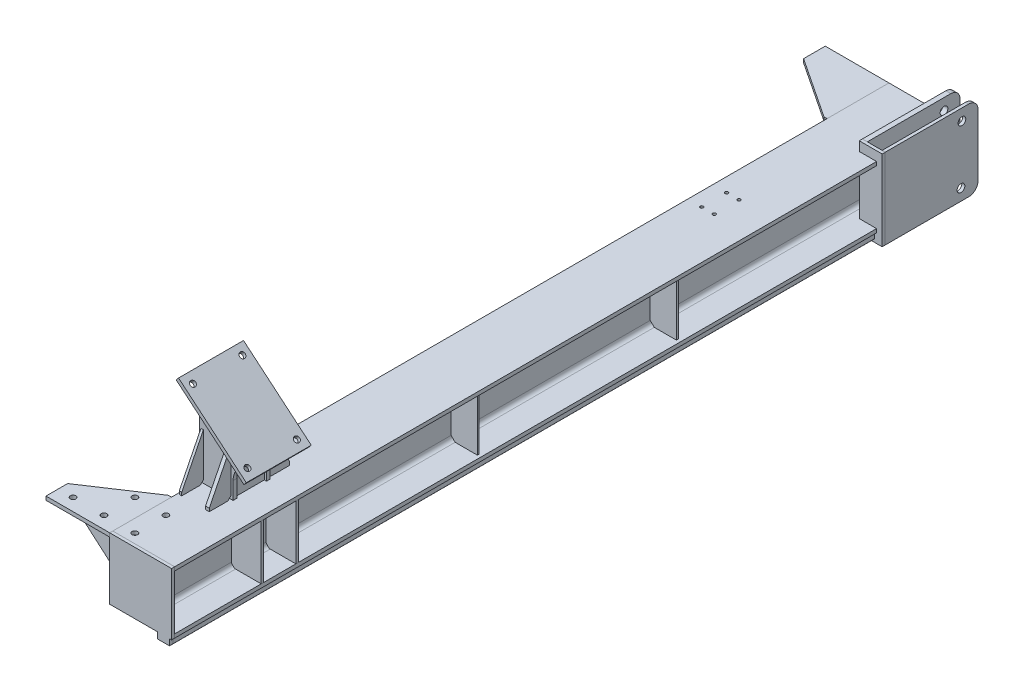
SolidWorks part; units mm, degrees
material "普通碳钢"
ref_plane "前视基准面" through (0, 0, 0) normal (0, 0, 1) x (1, 0, 0)
ref_plane "上视基准面" through (0, 0, 0) normal (0, 1, 0) x (1, 0, 0)
ref_plane "右视基准面" through (0, 0, 0) normal (1, 0, 0) x (0, 0, -1)
sketch "草图1" plane through (0, 0, 0) normal (1, 0, 0) x (0, 0, -1)
  line L0 (0, 0) -> (2410, 0)
  dimension "D1" = 2410
other "H型钢 HW200A(1)"
ref_plane "基准面1" through (0, 0, 0) normal (0, 0, -1) x (1, 0, 0)
sketch "草图14" plane through (0, 0, 0) normal (0, 0, -1) x (1, 0, 0)
  line L0 (-100, -100) -> (100, -100)
  line L1 (100, -100) -> (100, -88)
  line L2 (100, -88) -> (17, -88)
  line L3 (4, -75) -> (4, 75)
  line L4 (17, 88) -> (100, 88)
  line L5 (100, 88) -> (100, 100)
  line L6 (100, 100) -> (-100, 100)
  line L7 (0, 100) -> (0, -100) construction
  line L11 (0, 60) -> (0, 100) construction
  line L14 (-100, -100) -> (-100, -88)
  line L15 (-100, -88) -> (-17, -88)
  line L16 (-4, -75) -> (-4, 75)
  line L17 (-17, 88) -> (-100, 88)
  line L18 (-100, 88) -> (-100, 100)
  arc A2 (17, -88) -> (4, -75) centre (17, -75) cw
  arc A3 (4, 75) -> (17, 88) centre (17, 75) cw
  arc A5 (-17, -88) -> (-4, -75) centre (-17, -75) ccw
  arc A6 (-4, 75) -> (-17, 88) centre (-17, 75) ccw
  point P2 (0, 0)
  point P38 (0, 0)
  point P39 (100, 100)
  point P40 (100, -100)
  point P41 (-100, -100)
  dimension "D8" = 13
  dimension "D1" = 8
  dimension "D2" = 12
  dimension "D3" = 200
  dimension "D4" = 200
  dimension "D9" = 0
sketch "草图12" plane through (0, 100, 0) normal (0, 1, 0) x (1, 0, 0)
  line L4 (94, 2410) -> (94, 0)
  line L5 (94, 2410) -> (94, 0)
  dimension "D1" = 6
other "折弯轨道"
ref_plane "基准面2" through (94, 130, -2410) normal (0, 0, 1) x (1, 0, 0)
sketch "草图13" plane through (94, 130, -2410) normal (0, 0, 1) x (1, 0, 0)
  line L7 (-38, 0) -> (-2, 0)
  line L8 (-40, -2) -> (-40, -30)
  line L9 (0, -2) -> (0, -30)
  line L20 (-40, -30) -> (0, -30)
  line L21 (-194, 0) -> (6, 0) construction
  arc A7 (-2, 0) -> (0, -2) centre (-2, -2) cw
  arc A8 (-38, 0) -> (-40, -2) centre (-38, -2) ccw
  point P11 (25, 0)
  point P21 (0, 0)
  dimension "D4" = 2
  dimension "D1" = 30
  dimension "D2" = 40
  dimension "D5" = 6
mirror "镜向1" about plane through (0, 0, 0) normal (0, 1, 0) of bodies 108
sketch "草图16" plane through (0, 0, 0) normal (0, 0, 1) x (1, 0, 0)
  line L0 (94, -100) -> (100, -100)
  line L1 (-100, 100) -> (54, 100)
  line L2 (-100, 100) -> (-100, -100)
  line L3 (-100, -100) -> (54, -100)
  line L4 (100, 100) -> (100, -100)
  line L5 (94, -100) -> (94, -128)
  line L6 (94, 128) -> (94, 100)
  line L7 (54, 128) -> (54, 100)
  line L8 (94, 100) -> (100, 100)
  line L9 (92, 130) -> (56, 130) construction
  line L10 (54, 128) -> (54, 100) construction
  line L11 (100, -100) -> (-100, -100) construction
  line L12 (-100, 100) -> (100, 100) construction
  line L16 (92, 130) -> (56, 130)
  line L32 (92, -130) -> (56, -130)
  line L33 (54, -128) -> (54, -100)
  arc A0 (54, -128) -> (56, -130) centre (56, -128) ccw construction
  arc A1 (92, -130) -> (94, -128) centre (92, -128) ccw construction
  arc A2 (56, 130) -> (54, 128) centre (56, 128) ccw construction
  arc A3 (94, 128) -> (92, 130) centre (92, 128) ccw construction
  arc A4 (56, 130) -> (54, 128) centre (56, 128) ccw
  arc A7 (94, 128) -> (92, 130) centre (92, 128) ccw
  arc A17 (92, -130) -> (94, -128) centre (92, -128) ccw
  arc A18 (54, -128) -> (56, -130) centre (56, -128) ccw
  dimension "D1" = 30
extrude "凸台-拉伸1" add sketch "草图16" along normal blind 10 separate body contours L4 L0 L5 A17 L32 A18 L33 L3 L2 L1 L7 A4 L16 A7 L6 L8
sketch "草图17" plane through (0, 130, 0) normal (0, 1, 0) x (1, 0, 0)
  line L8 (-100, 2410) -> (100, 2410) construction
  line L9 (44, 2410) -> (100, 2410)
  line L11 (44, 2270) -> (100, 2270)
  line L12 (100, 2410) -> (100, 0) construction
  line L13 (100, 2410) -> (100, 2270)
  line L14 (44, 2354) -> (44, 0) construction
  line L15 (44, 2410) -> (44, 2270)
  line L17 (-100, 2410) -> (100, 2410) construction
  line L18 (-100, 2270) -> (100, 2270) construction
  line L19 (-100, 2354) -> (44, 2354) construction
  line L20 (100, 2410) -> (100, 0) construction
  dimension "D1" = 140
  dimension "D2" = 56
extrude "切除-拉伸1" cut sketch "草图17" against normal up to surface (260 mm away)
sketch "草图18" plane through (0, 130, 0) normal (0, 1, 0) x (1, 0, 0)
  line L0 (100, 2270) -> (100, 0) construction
  line L1 (44, 2580) -> (60, 2580)
  line L2 (44, 2580) -> (44, 2280)
  line L4 (60, 2580) -> (60, 2280)
  line L5 (100, 2270) -> (44, 2270) construction
  line L6 (44, 2280) -> (60, 2280)
  line L8 (118, 2280) -> (118, 2580)
  line L9 (118, 2580) -> (108, 2580)
  line L10 (108, 2280) -> (108, 2580)
  line L11 (108, 2280) -> (118, 2280)
  line L14 (44, 2270) -> (44, 2410) construction
  point P17 (34, 2400)
  dimension "D1" = 16
  dimension "D2" = 10
  dimension "D3" = 10
  dimension "D4" = 10
  dimension "D5" = 18
  dimension "D6" = 300
extrude "凸台-拉伸2" add sketch "草图18" against normal up to surface (260 mm away) separate body up to face at (74, -130, -1135)
fillet "圆角1" radius 30 2 edges at (113, -130, -2580) (113, 130, -2580)
fillet "圆角2" radius 30 2 edges at (52, -130, -2580) (52, 130, -2580)
sketch "草图19" plane through (0, 130, 0) normal (0, 1, 0) x (1, 0, 0)
  line L1 (44, 2280) -> (118, 2280)
  line L2 (44, 2280) -> (44, 2270)
  line L3 (44, 2270) -> (118, 2270)
  line L4 (118, 2280) -> (118, 2270)
  line L6 (100, 2270) -> (100, 0) construction
  line L7 (100, 2270) -> (44, 2270) construction
  dimension "D1" = 18
extrude "凸台-拉伸3" add sketch "草图19" against normal up to surface (260 mm away) separate body up to face at (74, -130, -1135)
sketch "草图20" plane through (118, 0, 0) normal (1, 0, 0) x (0, 0, -1)
  line L0 (2280, -130) -> (2280, 130) construction
  line L1 (2280, -130) -> (2280, 130) construction
  line L2 (2280, 130) -> (2550, 130) construction
  line L3 (2550, -130) -> (2280, -130) construction
  circle A0 centre (2528, 93) radius 12.5
  circle A1 centre (2525, -93) radius 12.5
  dimension "D1" = 248
  dimension "D3" = 25
  dimension "D4" = 25
  dimension "D2" = 245
  dimension "D5" = 37
  dimension "D6" = 37
extrude "切除-拉伸2" cut sketch "草图20" against normal up to surface (74 mm away) contours A1
ref_plane "基准面3" through (0, 0, -2480) normal (0, 0, -1) x (-1, 0, 0)
sketch "草图21" plane through (0, 0, -2480) normal (0, 0, -1) x (-1, 0, 0)
  line L0 (-60, 130) -> (-60, 100) construction
  line L1 (-60, 55) -> (-108, 55)
  line L2 (-60, 55) -> (-60, -55)
  line L3 (-60, -55) -> (-108, -55)
  line L4 (-108, 55) -> (-108, -55)
  line L5 (-108, -130) -> (-108, -100) construction
  line L6 (-118, 130) -> (-44, 130) construction
  line L7 (-118, 130) -> (-44, 130) construction
  line L8 (-44, -130) -> (-118, -130) construction
  line L9 (-44, -130) -> (-118, -130) construction
  dimension "D1" = 75
  dimension "D2" = 75
extrude "凸台-拉伸5" add sketch "草图21" against normal blind 8 separate body
ref_plane "基准面4" through (0, 0, -340) normal (0, 0, 1) x (1, 0, 0)
sketch "草图23" plane through (0, 0, -340) normal (0, 0, 1) x (1, 0, 0)
  line L6 (89.0887, 206.9702) -> (-130, 390.8075)
  line L7 (96.8022, 216.1627) -> (-122.2865, 400)
  line L8 (89.0887, 206.9702) -> (96.8022, 216.1627)
  line L9 (-130, 390.8075) -> (-122.2865, 400)
  line L11 (-100, 100) -> (44, 100) construction
  line L12 (-100, 100) -> (54, 100) construction
  line L13 (-100, 100) -> (-100, -100) construction
  dimension "D1" = 286
  dimension "D2" = 12
  dimension "D3" = 30
  dimension "D4" = 40
  dimension "D5" = 300
extrude "凸台-拉伸6" add sketch "草图23" along normal mid plane 210 separate body
sketch "草图25" plane through (146.4357, 174.5153, 0) normal (0.6428, 0.766, 0) x (0.766, -0.6428, 0)
  line L2 (-64.792, 420) -> (-350.792, 420)
  line L3 (-64.792, 420) -> (-350.792, 420) construction
  line L5 (-64.792, 260) -> (-350.792, 260)
  line L6 (-64.792, 260) -> (-350.792, 260) construction
  line L8 (-322.792, 235) -> (-322.792, 445)
  line L9 (-322.792, 235) -> (-322.792, 445) construction
  line L12 (-92.792, 235) -> (-92.792, 445)
  line L13 (-92.792, 235) -> (-92.792, 445) construction
  circle A0 centre (-322.792, 420) radius 9
  circle A1 centre (-92.792, 420) radius 9
  circle A2 centre (-92.792, 260) radius 9
  circle A3 centre (-322.792, 260) radius 9
  dimension "D5" = 18
  dimension "D6" = 18
  dimension "D7" = 18
  dimension "D8" = 18
  dimension "D1" = 25
  dimension "D2" = 25
  dimension "D3" = 28
  dimension "D4" = 28
extrude "切除-拉伸4" cut sketch "草图25" against normal up to next (12 mm away)
sketch "草图24" plane through (0, 0, -340) normal (0, 0, 1) x (1, 0, 0)
  line L0 (-100, 100) -> (54, 100) construction
  line L1 (2, 100) -> (-10, 100)
  line L2 (2, 100) -> (2, 280.0463)
  line L3 (-4, 285.0809) -> (-10, 285.0809)
  line L4 (-10, 100) -> (-10, 285.0809)
  line L5 (2, 280.0463) -> (-4, 285.0809)
  line L7 (-130, 390.8075) -> (89.0887, 206.9702) construction
  line L9 (-100, 88) -> (-100, 100) construction
  point P2 (2, 285.0809)
  dimension "D1" = 12
  dimension "D2" = 6
  dimension "D3" = 90
extrude "凸台-拉伸7" add sketch "草图24" along normal mid plane 96 separate body
sketch "草图26" plane through (0, 0, -388) normal (0, 0, -1) x (-1, 0, 0)
  line L0 (-59.0887, 232.1432) -> (100, 365.6345)
  line L1 (100, 365.6345) -> (100, 100)
  line L2 (-59.0887, 232.1432) -> (-59.0887, 154.6102) construction
  line L3 (130, 390.8075) -> (130, -58) construction
  line L4 (-89.0887, 206.9702) -> (-89.0887, 63.1666) construction
  line L5 (-44, 100) -> (-44, 297.8719) construction
  line L6 (-9, 100) -> (-9, 297.8719) construction
  line L8 (-9, 100) -> (100, 100)
  line L10 (100, 88) -> (17, 88)
  line L14 (17, -88) -> (100, -88)
  line L15 (17, 88) -> (4, 75)
  line L16 (4, 75) -> (4, -75)
  line L17 (4, -75) -> (17, -88)
  line L18 (130, 390.8075) -> (130, 142.1948) construction
  line L19 (130, 390.8075) -> (-89.0887, 206.9702) construction
  line L20 (-9, 100) -> (-9, 155.8505)
  line L21 (-25.7297, 197.4159) -> (-59.0887, 232.1432)
  line L22 (100, 88) -> (100, -88)
  arc A0 (-9, 155.8505) -> (-25.7297, 197.4159) centre (-69, 155.8505) ccw
  point P11 (-9, 180)
  dimension "D4" = 60
  dimension "D1" = 30
  dimension "D2" = 35
  dimension "D3" = 80
extrude "凸台-拉伸8" add sketch "草图26" along normal blind 12 separate body
sketch "草图27" plane through (0, 0, -292) normal (0, 0, 1) x (1, 0, 0)
  line L4 (25.7297, 197.4159) -> (59.0887, 232.1432)
  line L5 (59.0887, 232.1432) -> (-100, 365.6345)
  line L6 (-100, 88) -> (-100, -88)
  line L7 (-100, 88) -> (-100, -88)
  line L8 (-100, 365.6345) -> (-100, 100)
  line L9 (-100, 100) -> (9, 100)
  line L11 (59.0887, 232.1432) -> (-100, 365.6345)
  line L12 (-100, 365.6345) -> (-100, 100)
  line L13 (-100, -88) -> (-17, -88)
  line L14 (-17, -88) -> (-4, -75)
  line L15 (-4, -75) -> (-4, 75)
  line L16 (-4, 75) -> (-17, 88)
  line L17 (-17, 88) -> (-100, 88)
  line L18 (-100, 100) -> (9, 100)
  line L23 (-100, -88) -> (-17, -88)
  line L24 (-17, -88) -> (-4, -75)
  line L25 (-4, -75) -> (-4, 75)
  line L26 (-4, 75) -> (-17, 88)
  line L27 (-17, 88) -> (-100, 88)
  line L29 (25.7297, 197.4159) -> (59.0887, 232.1432)
  line L30 (9, 100) -> (9, 155.8505)
  line L31 (9, 100) -> (9, 155.8505)
  arc A1 (25.7297, 197.4159) -> (9, 155.8505) centre (69, 155.8505) ccw
  arc A2 (25.7297, 197.4159) -> (9, 155.8505) centre (69, 155.8505) ccw
  dimension "D1" = 0
  dimension "D2" = 0
extrude "凸台-拉伸11" add sketch "草图27" along normal blind 12 separate body contours L23 L24 L25 L26 L27 L7 | L11 L12 L18 L31 A2 L29
sketch "草图32" plane through (0, 0, 10) normal (0, 0, 1) x (1, 0, 0)
  line L0 (92, 130) -> (56, 130) construction
  line L1 (54, 100) -> (94, 100)
  line L2 (54, 100) -> (54, 130)
  line L3 (54, 130) -> (94, 130)
  line L4 (94, 100) -> (94, 130)
  line L5 (94, 128) -> (94, 100) construction
extrude "切除-拉伸9" cut sketch "草图32" against normal up to surface (2280 mm away) up to face at (81, 0, -2270)
sketch "草图33" plane through (0, 0, -2410) normal (0, 0, -1) x (-1, 0, 0)
  line L0 (-44, 100) -> (-44, 88)
  line L1 (-44, -88) -> (-44, -100)
  line L2 (-44, 100) -> (-44, 88) construction
  line L12 (100, 100) -> (-44, 100)
  line L13 (-44, 100) -> (-44, 88)
  line L14 (-44, 88) -> (-17, 88)
  line L15 (-4, 75) -> (-4, -75)
  line L16 (-17, -88) -> (-44, -88)
  line L17 (-44, -88) -> (-44, -100)
  line L18 (-44, -100) -> (100, -100)
  line L19 (100, -100) -> (100, -88)
  line L20 (100, -88) -> (17, -88)
  line L21 (4, -75) -> (4, 75)
  line L22 (17, 88) -> (100, 88)
  line L23 (100, 88) -> (100, 100)
  line L24 (100, 100) -> (-44, 100)
  line L26 (-44, 88) -> (-17, 88)
  line L27 (-4, 75) -> (-4, -75)
  line L28 (-17, -88) -> (-44, -88)
  line L30 (-44, -100) -> (100, -100)
  line L31 (100, -100) -> (100, -88)
  line L32 (100, -88) -> (17, -88)
  line L33 (4, -75) -> (4, 75)
  line L34 (17, 88) -> (100, 88)
  line L35 (100, 88) -> (100, 100)
  arc A4 (-4, 75) -> (-17, 88) centre (-17, 75) ccw
  arc A5 (-17, -88) -> (-4, -75) centre (-17, -75) ccw
  arc A6 (4, -75) -> (17, -88) centre (17, -75) ccw
  arc A7 (17, 88) -> (4, 75) centre (17, 75) ccw
  arc A8 (-4, 75) -> (-17, 88) centre (-17, 75) ccw
  arc A9 (-17, -88) -> (-4, -75) centre (-17, -75) ccw
  arc A10 (4, -75) -> (17, -88) centre (17, -75) ccw
  arc A11 (17, 88) -> (4, 75) centre (17, 75) ccw
  dimension "D1" = 0
extrude "凸台-拉伸12" add sketch "草图33" along normal blind 100
sketch "草图34" plane through (0, 88, 0) normal (0, -1, 0) x (1, 0, 0)
  line L0 (-306, 10) -> (-100, 10)
  line L1 (-100, 10) -> (-100, -190)
  line L2 (-100, -2510) -> (-100, 0) construction
  line L3 (-100, -190) -> (-110, -190)
  line L4 (-110, -190) -> (-306, -60)
  line L5 (-306, -60) -> (-306, 10)
  line L6 (-100, 10) -> (100, 10) construction
  dimension "D1" = 200
  dimension "D2" = 10
  dimension "D3" = 206
  dimension "D4" = 70
extrude "凸台-拉伸13" add sketch "草图34" against normal up to surface (12 mm away) separate body up to face at (14.6667, 100, -1593.3333)
sketch "草图35" plane through (0, 88, 0) normal (0, -1, 0) x (1, 0, 0)
  line L0 (-100, -2510) -> (-306, -2510)
  line L1 (-100, -2510) -> (-100, 0) construction
  line L2 (-306, -2510) -> (-306, -2440)
  line L3 (-306, -2440) -> (-110, -2310)
  line L4 (-110, -2310) -> (-100, -2310)
  line L5 (-100, -2310) -> (-100, -2510)
  line L6 (-17, -2510) -> (-100, -2510) construction
  dimension "D1" = 200
  dimension "D2" = 10
  dimension "D3" = 206
  dimension "D4" = 70
extrude "凸台-拉伸14" add sketch "草图35" against normal up to surface (12 mm away) separate body up to face at (14.6667, 100, -1593.3333)
ref_plane "基准面5" through (0, 0, -60) normal (0, 0, 1) x (1, 0, 0)
sketch "草图36" plane through (0, 0, -60) normal (0, 0, 1) x (1, 0, 0)
  line L4 (-17, 88) -> (-100, 88) construction
  line L5 (-95, 88) -> (-297, 88)
  line L9 (-95, 88) -> (-95, -88)
  line L10 (-95, -88) -> (-105, -88)
  line L11 (-105, -88) -> (-297, 78)
  line L12 (-100, 100) -> (-100, -100) construction
  line L13 (-100, -88) -> (-17, -88) construction
  line L24 (-297, 88) -> (-297, 78)
  dimension "D2" = 10
  dimension "D1" = 280
  dimension "D3" = 10
  dimension "D4" = 5
extrude "凸台-拉伸15" add sketch "草图36" along normal blind 10 separate body
ref_plane "基准面6" through (0, 0, -2440) normal (0, 0, -1) x (-1, 0, 0)
sketch "草图37" plane through (0, 0, -2440) normal (0, 0, -1) x (-1, 0, 0)
  line L5 (95, 88) -> (95, -88)
  line L6 (95, 88) -> (95, -88)
  line L7 (95, -88) -> (105, -88)
  line L8 (95, -88) -> (105, -88)
  line L9 (105, -88) -> (297, 78)
  line L10 (105, -88) -> (297, 78)
  line L12 (297, 78) -> (297, 88)
  line L13 (297, 88) -> (95, 88)
  line L19 (297, 78) -> (297, 88)
  line L20 (297, 88) -> (95, 88)
  dimension "D1" = 0
extrude "凸台-拉伸16" add sketch "草图37" along normal blind 10 separate body
sketch "草图38" plane through (0, 88, 0) normal (0, -1, 0) x (-1, 0, 0)
  line L0 (-47.2565, 2470) -> (306, 2470) construction
  line L1 (306, 2440) -> (306, 2510) construction
  line L2 (306, 2510) -> (100, 2510) construction
  line L4 (58.5, 2510) -> (58.5, 2450) construction
  line L5 (17, 2510) -> (100, 2510) construction
  line L6 (297, 2450) -> (95, 2450) construction
  line L7 (158.5, 2510) -> (158.5, 2342.1684) construction
  line L8 (258.5, 2510) -> (258.5, 2450) construction
  line L9 (-47.2565, 2370) -> (306, 2370) construction
  line L10 (58.5, 2450) -> (58.5, 2313.7396) construction
  line L11 (110, 2310) -> (306, 2440) construction
  circle A0 centre (58.5, 2470) radius 9
  circle A1 centre (158.5, 2470) radius 9
  circle A2 centre (258.5, 2470) radius 9
  circle A3 centre (58.5, 2370) radius 9
  circle A4 centre (158.5, 2370) radius 9
  dimension "D4" = 18
  dimension "D5" = 18
  dimension "D6" = 18
  dimension "D8" = 18
  dimension "D9" = 18
  dimension "D1" = 40
  dimension "D2" = 100
  dimension "D3" = 100
  dimension "D7" = 100
extrude "切除-拉伸10" cut sketch "草图38" against normal blind 10
sketch "草图39" plane through (0, 88, 0) normal (0, -1, 0) x (1, 0, 0)
  line L0 (-17, -30) -> (-306, -30) construction
  line L1 (-17, -2510) -> (-17, 0) construction
  line L2 (-306, 10) -> (-306, -60) construction
  line L3 (-17, -130) -> (-200.4615, -130) construction
  line L4 (-306, -60) -> (-110, -190) construction
  line L5 (-58.5, 0) -> (-58.5, -170.5835) construction
  line L6 (-17, 0) -> (-100, 0) construction
  line L8 (-158.5, 10) -> (-158.5, -158.7816) construction
  line L9 (-100, 10) -> (-306, 10) construction
  line L10 (-258.5, 10) -> (-258.5, -80.1176) construction
  circle A0 centre (-258.5, -30) radius 9
  circle A1 centre (-158.5, -30) radius 9
  circle A2 centre (-58.5, -30) radius 9
  circle A3 centre (-58.5, -130) radius 9
  circle A4 centre (-158.5, -130) radius 9
  dimension "D5" = 18
  dimension "D6" = 18
  dimension "D7" = 18
  dimension "D8" = 18
  dimension "D9" = 18
  dimension "D1" = 100
  dimension "D2" = 40
  dimension "D3" = 100
  dimension "D4" = 100
extrude "切除-拉伸11" cut sketch "草图39" against normal up to surface (12 mm away) up to face at (14.6667, 100, -1593.3333)
ref_plane "基准面7" through (0, 0, -990) normal (0, 0, 1) x (1, 0, 0)
sketch "草图41" plane through (0, 0, -990) normal (0, 0, 1) x (1, 0, 0)
  line L0 (17, -88) -> (100, -88) construction
  line L1 (17, -88) -> (89, -88)
  line L2 (4, 75) -> (4, -75) construction
  line L3 (4, 75) -> (4, -75)
  line L4 (100, 88) -> (17, 88) construction
  line L5 (89, 88) -> (17, 88)
  line L6 (17, 88) -> (4, 75)
  line L7 (4, -75) -> (17, -88)
  line L8 (89, 88) -> (89, -88)
  dimension "D1" = 85
extrude "凸台-拉伸18" add sketch "草图41" against normal blind 6 separate body
ref_plane "基准面8" through (0, 0, -1640) normal (0, 0, 1) x (1, 0, 0)
sketch "草图42" plane through (0, 0, -1640) normal (0, 0, 1) x (1, 0, 0)
  line L6 (4, -75) -> (17, -88)
  line L7 (4, 75) -> (4, -75)
  line L8 (17, 88) -> (4, 75)
  line L9 (89, 88) -> (17, 88)
  line L10 (89, -88) -> (89, 88)
  line L11 (17, -88) -> (89, -88)
  line L12 (4, -75) -> (17, -88)
  line L13 (4, 75) -> (4, -75)
  line L14 (17, 88) -> (4, 75)
  line L15 (89, 88) -> (17, 88)
  line L16 (89, -88) -> (89, 88)
  line L17 (17, -88) -> (89, -88)
  dimension "D1" = 0
extrude "凸台-拉伸19" add sketch "草图42" along normal blind 6 separate body
sketch "草图43" plane through (0, 100, 0) normal (0, 1, 0) x (1, 0, 0)
  line L0 (-55, 1940) -> (-55, 1860) construction
  line L1 (-15, 1940) -> (-15, 1860) construction
  line L2 (-15, 1940) -> (-55, 1940) construction
  line L3 (-15, 1860) -> (-55, 1860) construction
  line L5 (-15, 1895.3947) -> (-15, 1468.073) construction
  line L6 (-55, 1895.3947) -> (-55, 1468.073) construction
  line L7 (-100, 2510) -> (-100, 0) construction
  line L8 (-100, 2510) -> (44, 2510) construction
  circle A0 centre (-15, 1940) radius 5
  circle A1 centre (-55, 1940) radius 5
  circle A3 centre (-55, 1860) radius 5
  circle A4 centre (-15, 1860) radius 5
  dimension "D2" = 10
  dimension "D1" = 40
  dimension "D3" = 45
  dimension "D4" = 80
  dimension "D5" = 650
extrude "切除-拉伸12" cut sketch "草图43" against normal up to surface (12 mm away) up to face at (-49.5, 88, -30)
sketch "草图112" plane through (0, -130, 0) normal (0, -1, 0) x (1, 0, 0)
  line L0 (92, 0) -> (56, 0) construction
  line L1 (118, -2270) -> (44, -2270)
  line L2 (118, -2270) -> (118, 0)
  line L3 (118, 0) -> (44, 0)
  line L4 (44, -2270) -> (44, 0)
extrude "切除-拉伸13" cut sketch "草图112" against normal up to surface (30 mm away) up to face at (14.6667, -100, -1593.3333)
sketch "草图113" plane through (0, 0, 0) normal (0, 0, -1) x (-1, 0, 0)
  line L0 (-54, -128) -> (-54, -100) construction
  line L1 (-94, -100) -> (-54, -100)
  line L2 (-94, -100) -> (-94, -119)
  line L3 (-93, -120) -> (-55, -120)
  line L4 (-54, -100) -> (-54, -119)
  arc A0 (-94, -119) -> (-93, -120) centre (-93, -119) ccw
  arc A1 (-55, -120) -> (-54, -119) centre (-55, -119) ccw
  point P13 (-54, -120)
  dimension "D1" = 1
  dimension "D4" = 20
extrude "凸台-拉伸20" add sketch "草图113" along normal up to surface (2270 mm away) separate body up to face at (81, 0, -2270)
sketch "草图114" plane through (0, 0, 0) normal (0, 0, -1) x (-1, 0, 0)
  line L0 (-92, -130) -> (-56, -130) construction
  line L1 (-92, -130) -> (-56, -130)
  line L2 (-54, -128) -> (-54, -100) construction
  line L3 (-54, -128) -> (-54, -119)
  line L4 (-94, -100) -> (-94, -128) construction
  line L5 (-94, -119) -> (-94, -128)
  line L6 (-93, -120) -> (-55, -120) construction
  line L7 (-93, -120) -> (-55, -120)
  arc A0 (-56, -130) -> (-54, -128) centre (-56, -128) ccw construction
  arc A1 (-56, -130) -> (-54, -128) centre (-56, -128) ccw
  arc A2 (-94, -128) -> (-92, -130) centre (-92, -128) ccw construction
  arc A3 (-94, -128) -> (-92, -130) centre (-92, -128) ccw
  arc A4 (-55, -120) -> (-54, -119) centre (-55, -119) ccw construction
  arc A5 (-55, -120) -> (-54, -119) centre (-55, -119) ccw
  arc A6 (-94, -119) -> (-93, -120) centre (-93, -119) ccw construction
  arc A7 (-94, -119) -> (-93, -120) centre (-93, -119) ccw
extrude "切除-拉伸14" cut sketch "草图114" against normal blind 10
ref_plane "基准面9" through (-95, 0, 0) normal (-1, 0, 0) x (0, 0, 1)
sketch "草图115" plane through (-95, 0, 0) normal (-1, 0, 0) x (0, 0, 1)
  line L1 (-388, 88) -> (-292, 88)
  line L2 (-388, 88) -> (-388, -88)
  line L3 (-388, -88) -> (-292, -88)
  line L4 (-292, 88) -> (-292, -88)
  line L5 (-280, 88) -> (0, 88)
  line L6 (-280, 88) -> (-280, -88)
  line L7 (-280, -88) -> (0, -88)
  line L8 (0, 88) -> (0, -88)
  line L9 (-400, 88) -> (-600, 88)
  line L10 (-400, 88) -> (-400, -88)
  line L11 (-400, -88) -> (-600, -88)
  line L12 (-600, 88) -> (-600, -88)
  dimension "D1" = 200
extrude "凸台-拉伸21" add sketch "草图115" against normal blind 8 separate body
sketch "草图116" plane through (-95, 0, 0) normal (-1, 0, 0) x (0, 0, 1)
  line L1 (-388, 100) -> (-292, 100)
  line L2 (-388, 100) -> (-388, 361.439)
  line L3 (-388, 361.439) -> (-292, 361.439)
  line L4 (-292, 100) -> (-292, 361.439)
extrude "凸台-拉伸22" add sketch "草图116" against normal blind 8 separate body
sketch "草图118" plane through (0, 0, -400) normal (0, 0, -1) x (-1, 0, 0)
  line L0 (-4, 75) -> (-4, -75) construction
  line L1 (-100, 88) -> (-14, 88)
  line L2 (-100, 88) -> (-100, -88)
  line L3 (-100, -88) -> (-14, -88)
  line L4 (-4, 78) -> (-4, -78)
  line L5 (-14, 88) -> (-4, 78)
  line L6 (-14, -88) -> (-4, -78)
  point P1 (-4, -88)
  point P3 (-4, 88)
extrude "凸台-拉伸23" add sketch "草图118" against normal blind 8 separate body
sketch "草图119" plane through (0, 0, -280) normal (0, 0, 1) x (1, 0, 0)
  line L6 (100, -88) -> (100, 88)
  line L7 (100, 88) -> (14, 88)
  line L8 (14, 88) -> (4, 78)
  line L9 (4, 78) -> (4, -78)
  line L10 (4, -78) -> (14, -88)
  line L11 (14, -88) -> (100, -88)
  line L12 (100, -88) -> (100, 88)
  line L13 (100, 88) -> (14, 88)
  line L14 (14, 88) -> (4, 78)
  line L15 (4, 78) -> (4, -78)
  line L16 (4, -78) -> (14, -88)
  line L17 (14, -88) -> (100, -88)
  dimension "D1" = 0
extrude "凸台-拉伸24" add sketch "草图119" against normal blind 8 separate body
sketch "草图120" plane through (2, 0, 0) normal (1, 0, 0) x (0, 0, -1)
  line L0 (280, 110) -> (280, 250)
  line L1 (280, 250) -> (210, 110)
  line L2 (210, 110) -> (210, 100)
  line L3 (210, 100) -> (270, 100)
  line L4 (340, 100) -> (340, 306.3113) construction
  line L5 (292, 100) -> (388, 100) construction
  line L6 (470, 100) -> (410, 100)
  line L7 (470, 110) -> (470, 100)
  line L8 (400, 250) -> (470, 110)
  line L9 (400, 110) -> (400, 250)
  line L10 (270, 100) -> (280, 110)
  line L11 (410, 100) -> (400, 110)
  point P2 (280, 100)
  point P10 (400, 100)
  dimension "D1" = 70
  dimension "D2" = 10
  dimension "D3" = 150
extrude "凸台-拉伸25" add sketch "草图120" against normal blind 12 separate body
sketch "草图122" plane through (-95, 0, 0) normal (-1, 0, 0) x (0, 0, 1)
  line L5 (-470, 110) -> (-470, 100)
  line L6 (-470, 100) -> (-410, 100)
  line L7 (-410, 100) -> (-400, 110)
  line L8 (-400, 110) -> (-400, 250)
  line L9 (-400, 250) -> (-470, 110)
  line L10 (-470, 110) -> (-470, 100)
  line L11 (-470, 100) -> (-410, 100)
  line L12 (-410, 100) -> (-400, 110)
  line L13 (-400, 110) -> (-400, 250)
  line L14 (-400, 250) -> (-470, 110)
  line L15 (-210, 110) -> (-280, 250)
  line L16 (-280, 250) -> (-280, 110)
  line L17 (-280, 110) -> (-270, 100)
  line L18 (-270, 100) -> (-210, 100)
  line L19 (-210, 100) -> (-210, 110)
  line L20 (-210, 110) -> (-280, 250)
  line L21 (-280, 250) -> (-280, 110)
  line L22 (-280, 110) -> (-270, 100)
  line L23 (-270, 100) -> (-210, 100)
  line L24 (-210, 100) -> (-210, 110)
  dimension "D1" = 0
  dimension "D2" = 0
extrude "凸台-拉伸26" add sketch "草图122" against normal blind 8 separate body
sketch "草图123" plane through (-95, 0, 0) normal (-1, 0, 0) x (0, 0, 1)
  line L0 (-2510, 88) -> (0, 88) construction
  line L1 (-2510, -88) -> (-2310, -88)
  line L2 (-2510, -88) -> (-2510, 88)
  line L3 (-2510, 88) -> (-2310, 88)
  line L4 (-2310, -88) -> (-2310, 88)
  line L5 (-1610, 88) -> (-1310, 88)
  line L6 (-1610, 88) -> (-1610, -88)
  line L7 (-1610, -88) -> (-1310, -88)
  line L8 (-1310, 88) -> (-1310, -88)
  line L9 (-2510, -88) -> (0, -88) construction
  dimension "D1" = 200
  dimension "D2" = 700
  dimension "D3" = 300
extrude "凸台-拉伸27" add sketch "草图123" against normal blind 8 separate body
